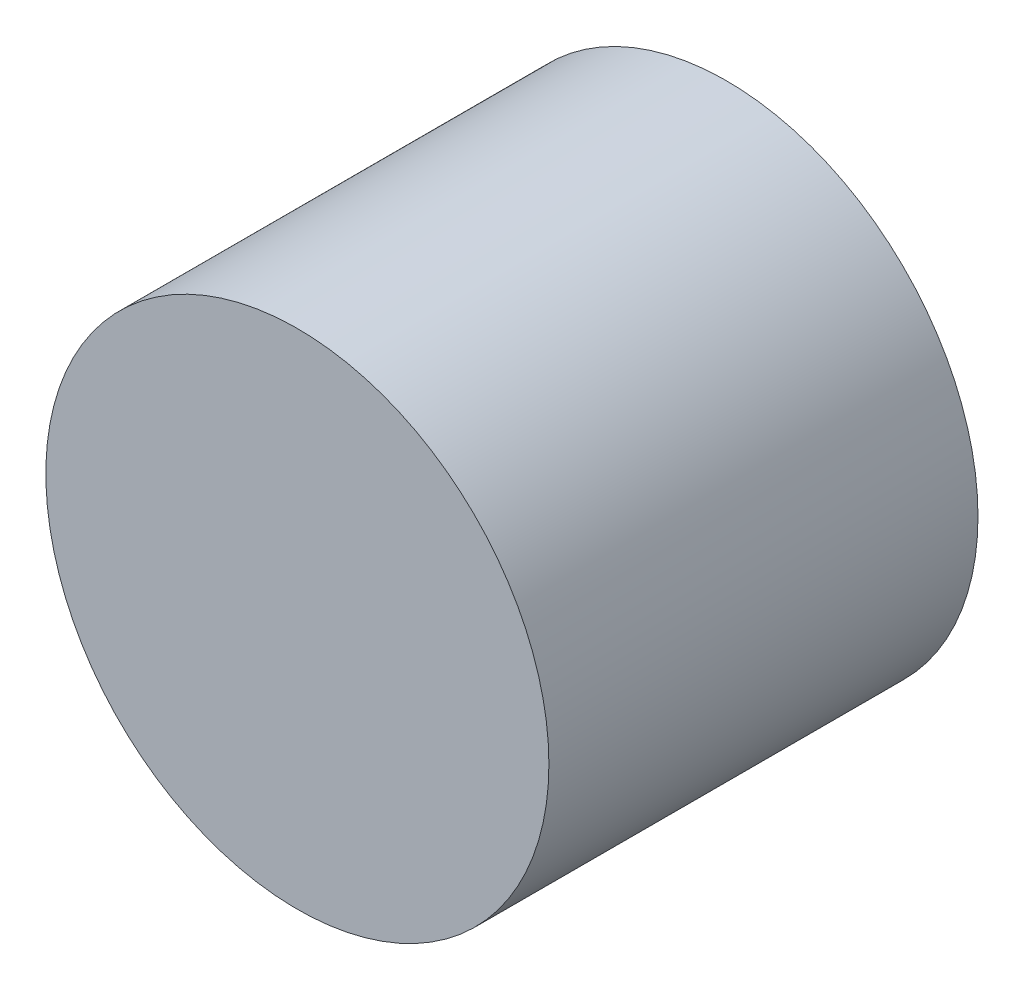
SolidWorks part; units mm, degrees
ref_plane "Front Plane" through (0, 0, 0) normal (0, 0, 1) x (1, 0, 0)
ref_plane "Top Plane" through (0, 0, 0) normal (0, 1, 0) x (1, 0, 0)
ref_plane "Right Plane" through (0, 0, 0) normal (1, 0, 0) x (0, 0, -1)
sketch "Sketch1" plane through (0, 0, 0) normal (0, 0, 1) x (1, 0, 0)
  circle A0 centre (0, 0) radius 8.5
  dimension "D1" = 17
extrude "Boss-Extrude1" add sketch "Sketch1" along normal blind 14.5
